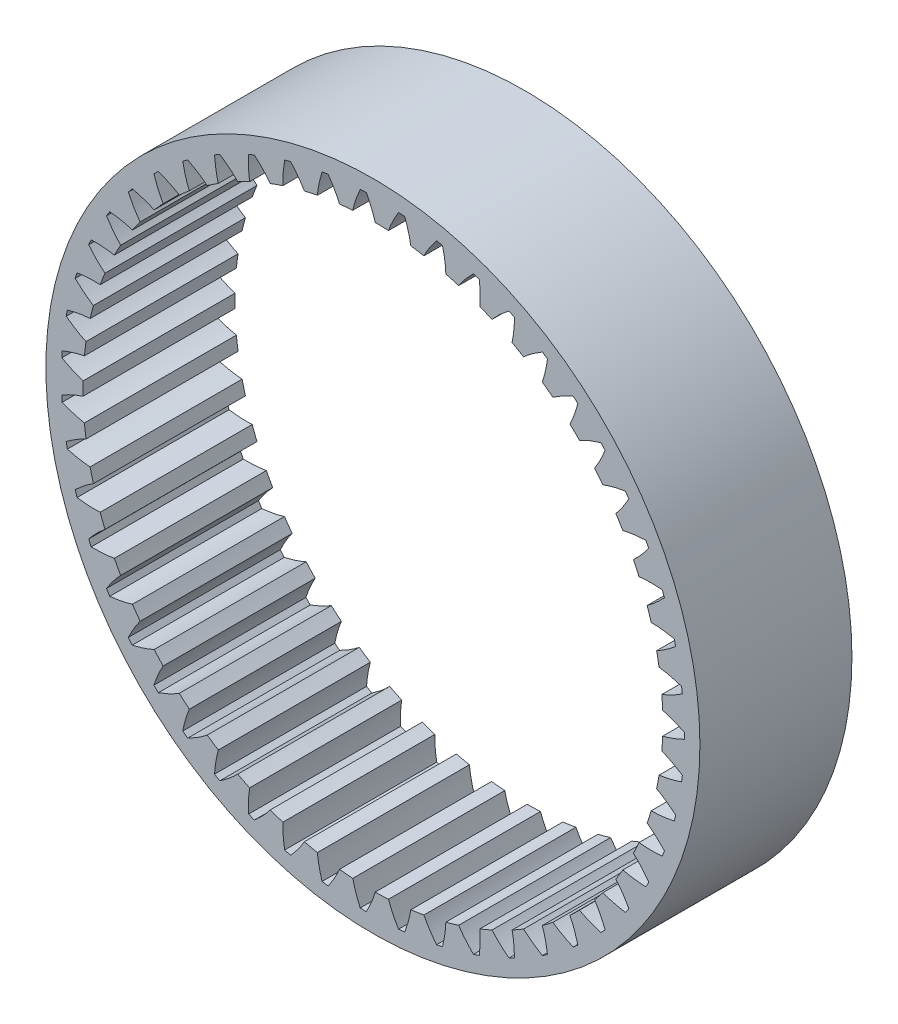
SolidWorks part; units mm, degrees
ref_plane "Front Plane" through (0, 0, 0) normal (0, 0, 1) x (1, 0, 0)
ref_plane "Top Plane" through (0, 0, 0) normal (0, 1, 0) x (1, 0, 0)
ref_plane "Right Plane" through (0, 0, 0) normal (1, 0, 0) x (0, 0, -1)
ref_axis "Axis1" through (0, 0, 6.9289) along (0, 0, -1)
sketch "Sketch3" plane through (0, 0, 0) normal (0, 0, 1) x (1, 0, 0)
  circle A0 centre (0, 0) radius 14.4132
  circle A1 centre (0, 0) radius 12.7793
  dimension "D1" = 28.8263
  dimension "D2" = 25.5585
extrude "Boss-Extrude2" add sketch "Sketch3" along normal blind 6.7
sketch "Sketch1" plane through (0, 0, 0) normal (0, 0, 1) x (1, 0, 0)
  line L8 (13.7262, 0.1357) -> (13.7262, -0.1357)
  line L10 (12.7697, 0.494) -> (12.7697, -0.494)
  circle A0 centre (0, 0) radius 12.7793 construction
  circle A1 centre (0, 0) radius 12.2733 construction
  circle A4 centre (0, 0) radius 13.7268 construction
  spline S0 degree 4 poles (12.6989, 0.5109) (12.704, 0.5097) (12.7137, 0.5075) (12.7273, 0.5044) (12.7616, 0.4961) (12.7786, 0.4918) (12.8216, 0.4809) (12.8476, 0.4738) (12.883, 0.464) (12.9127, 0.4555) (12.9457, 0.4458) (12.9766, 0.4364) (13.0087, 0.4264) (13.0399, 0.4163) (13.0716, 0.4059) (13.1027, 0.3954) (13.1342, 0.3846) (13.1723, 0.3711) (13.2188, 0.3542) (13.2716, 0.3344) (13.3337, 0.31) (13.3933, 0.286) (13.4571, 0.259) (13.5133, 0.2349) (13.5812, 0.2042) (13.629, 0.1825) (13.7046, 0.1463) (13.737, 0.1305) (13.7859, 0.1062) (13.8062, 0.0959) (13.8175, 0.0901) knots 0 0 0 0 0 0.01522 0.030441 0.060378 0.088008 0.115638 0.143268 0.170897 0.198527 0.226157 0.253787 0.281417 0.309046 0.336676 0.364306 0.391936 0.419565 0.472504 0.527763 0.583023 0.638282 0.693542 0.748801 0.804061 0.85932 0.91458 0.95729 1 1 1 1 1 construction
  spline S1 degree 4 poles (12.7697, 0.494) (12.7766, 0.4923) (12.79, 0.4889) (12.8216, 0.4809) (12.8476, 0.4738) (12.883, 0.464) (12.9127, 0.4555) (12.9457, 0.4458) (12.9766, 0.4364) (13.0087, 0.4264) (13.0399, 0.4163) (13.0716, 0.4059) (13.1027, 0.3954) (13.1342, 0.3846) (13.1723, 0.3711) (13.2188, 0.3542) (13.2716, 0.3344) (13.3337, 0.31) (13.3933, 0.286) (13.4571, 0.259) (13.5133, 0.2349) (13.5812, 0.2042) (13.629, 0.1825) (13.6891, 0.1537) (13.7135, 0.1419) (13.7262, 0.1357) knots 0.060378 0.060378 0.060378 0.060378 0.060378 0.088008 0.115638 0.143268 0.170897 0.198527 0.226157 0.253787 0.281417 0.309046 0.336676 0.364306 0.391936 0.419565 0.472504 0.527763 0.583023 0.638282 0.693542 0.748801 0.804061 0.85932 0.91458 0.91458 0.91458 0.91458 0.91458
  spline S2 degree 4 poles (12.6989, -0.5109) (12.704, -0.5097) (12.7137, -0.5075) (12.7273, -0.5044) (12.7616, -0.4961) (12.7786, -0.4918) (12.8216, -0.4809) (12.8476, -0.4738) (12.883, -0.464) (12.9127, -0.4555) (12.9457, -0.4458) (12.9766, -0.4364) (13.0087, -0.4264) (13.0399, -0.4163) (13.0716, -0.4059) (13.1027, -0.3954) (13.1342, -0.3846) (13.1723, -0.3711) (13.2188, -0.3542) (13.2716, -0.3344) (13.3337, -0.31) (13.3933, -0.286) (13.4571, -0.259) (13.5133, -0.2349) (13.5812, -0.2042) (13.629, -0.1825) (13.7046, -0.1463) (13.737, -0.1305) (13.7859, -0.1062) (13.8062, -0.0959) (13.8175, -0.0901) knots 0 0 0 0 0 0.01522 0.030441 0.060378 0.088008 0.115638 0.143268 0.170897 0.198527 0.226157 0.253787 0.281417 0.309046 0.336676 0.364306 0.391936 0.419565 0.472504 0.527763 0.583023 0.638282 0.693542 0.748801 0.804061 0.85932 0.91458 0.95729 1 1 1 1 1 construction
  spline S3 degree 4 poles (12.7697, -0.494) (12.7766, -0.4923) (12.79, -0.4889) (12.8216, -0.4809) (12.8476, -0.4738) (12.883, -0.464) (12.9127, -0.4555) (12.9457, -0.4458) (12.9766, -0.4364) (13.0087, -0.4264) (13.0399, -0.4163) (13.0716, -0.4059) (13.1027, -0.3954) (13.1342, -0.3846) (13.1723, -0.3711) (13.2188, -0.3542) (13.2716, -0.3344) (13.3337, -0.31) (13.3933, -0.286) (13.4571, -0.259) (13.5133, -0.2349) (13.5812, -0.2042) (13.629, -0.1825) (13.6891, -0.1537) (13.7135, -0.1419) (13.7262, -0.1357) knots 0.060378 0.060378 0.060378 0.060378 0.060378 0.088008 0.115638 0.143268 0.170897 0.198527 0.226157 0.253787 0.281417 0.309046 0.336676 0.364306 0.391936 0.419565 0.472504 0.527763 0.583023 0.638282 0.693542 0.748801 0.804061 0.85932 0.91458 0.91458 0.91458 0.91458 0.91458
  dimension "D1" = 25.5585
  dimension "D2" = 24.5466
  dimension "D3" = 27.4537
extrude "Cut-Extrude2" cut sketch "Sketch1" along normal through all
pattern_circular "CirPattern1" count 51 over 360 about axis through (0, 0, 6.9289) along (0, 0, -1) of "Cut-Extrude2"
sketch "Sketch4" plane through (0, 0, 0) normal (0, 0, 1) x (1, 0, 0)
  circle A0 centre (0, 0) radius 15
  circle A1 centre (0, 0) radius 14.4132
  dimension "D1" = 30
  dimension "D2" = 28.8263
extrude "width match" [suppressed] add sketch "Sketch4" along normal up to surface (6.7 mm away)
sketch "Sketch5" plane through (0, 0, 0) normal (0, 1, 0) x (1, 0, 0)
  line L0 (0, -6.9289) -> (0, 0.335) construction
  line L1 (10, -6.7) -> (15, -6.7)
  line L2 (10, -6.7) -> (10, -4.7)
  line L3 (10, -4.7) -> (15, -4.7)
  line L4 (15, -6.7) -> (15, -4.7)
  line L5 (15, 0) -> (16, 0)
  line L6 (15, 0) -> (15, -1)
  line L7 (15, -1) -> (16, -1)
  line L8 (16, 0) -> (16, -1)
  dimension "D1" = 15
  dimension "D2" = 1
  dimension "D3" = 1
  dimension "D4" = 15
  dimension "D5" = 6.7
  dimension "D6" = 4.7
  dimension "D7" = 5
revolve "Revolve1" [suppressed] add sketch "Sketch5" angle 360 about axis through (0, 0, 6.9289) along (0, 0, -1)
sketch "Sketch6" plane through (0, 0, 0) normal (0, 1, 0) x (1, 0, 0)
  line L0 (0, -6.9289) -> (0, 0.335) construction
  line L1 (14.75, -5.7) -> (15, -5.7)
  line L2 (14.75, -5.7) -> (14.75, -4.7)
  line L3 (14.75, -4.7) -> (15, -4.7)
  line L4 (15, -5.7) -> (15, -4.7)
  dimension "D1" = 4.7
  dimension "D2" = 1
  dimension "D3" = 0.25
  dimension "D4" = 15
revolve "Cut-Revolve1" [suppressed] cut sketch "Sketch6" angle 360 about axis through (0, 0, 6.9289) along (0, 0, -1)
sketch "Sketch7" [suppressed] plane through (0, 0, 6.7) normal (0, 0, 1) x (1, 0, 0)
  line L0 (0, 0) -> (12, 0) construction
  dimension "D1" = 12
sketch "Sketch8" [suppressed] plane through (0, 0, 6.7) normal (0, 0, 1) x (1, 0, 0)
  point P0 (12, 0)
hole_wizard "Tap Drill for M2x0.4 Tap1" [suppressed] positions "Sketch8" profile "Sketch9" hole size "M2x0.4" standard "ANSI Metric"
sketch "Sketch9" plane through (12, 0, 6.7) normal (1, 0, 0) x (0, -1, 0)
  line L0 (0, 0) -> (0, 6.7)
  line L1 (0, 6.7) -> (0.8, 6.7)
  line L2 (0.8, 6.7) -> (0.8, 0)
  line L5 (0.8, 0) -> (0, 0)
  line L11 (0, -6.35) -> (0, 107.95) construction
  dimension "Thru Hole Dia." = 1.6
  dimension "Thru Hole Depth" = 6.7
pattern_circular "CirPattern2" [suppressed] count 6 over 360 about axis through (0, 0, 6.9289) along (0, 0, -1)
equation "\"S1_Module\"= 0.5\t\t'tooth per mm"
equation "\"R1_NumTeeth\"= 52"
equation "\"R2_teeth\"= 51"
equation "\"P1_teeth\"= 10"
equation "\"S1_PressureAngle\"= 20'deg. leave unitless"
equation "\"sun_teeth\"= \"R1_NumTeeth\" - 2 * \"P1_teeth\""
equation "\"S2_Module\"= 0.5121951219512195\t\t\t'stage two gear modules CAN be different from stage 1; this makes things a lot more complicated though so try and avoid it if you can"
equation "\"S2_PressureAngle\"= \"S1_PressureAngle\"'stage two pressure angle can be different, but for simplicity keep it the same"
equation "\"S1_carrier_radius\"= \"P1_teeth\" * \"S1_Module\" / 2  + \"sun_teeth\" * \"S1_Module\" / 2"
equation "\"P2_teeth\" = 10"
equation "\"Ring_profile_shift\" = 0.05"
equation "\"Planet_profile_shift\" = -0.05"
equation "\"Planet_broachcutter_offset\" = -0.0"
equation "\"Ring_broachcutter_offset\" = 0.0"
equation "\"Nteeth_bcg\"= \"R2_teeth\""
equation "\"module\"= \"S2_Module\""
equation "\"x_shift\"= \"Ring_profile_shift\""
equation "\"r_p_bcg\"= \"module\" * \"Nteeth_bcg\" / 2"
equation "\"head\"= - 0.4 'Default. A clearance parameter applied to the addendum in internal gears. Removes material for clearance"
equation "\"r_a_bcg\"= \"r_p_bcg\" - \"module\" * ( 1 - \"x_shift\" + \"head\" )"
equation "\"r_f_bcg\"= \"r_p_bcg\" + \"module\" * ( 1.25 + \"x_shift\" )"
equation "\"Nteeth\"= \"R2_teeth\""
equation "\"pressure_angle\"= \"S1_PressureAngle\" * pi / 180"
equation "\"r_p\"= \"module\" * \"Nteeth\" / 2'pitch circle radius"
equation "\"r_b\"= \"r_p\" * cos ( \"pressure_angle\" )'base circle radius"
equation "\"r_f\"= \"r_p\" + \"module\" * ( 1.25 + \"x_shift\" )"
equation "\"r_a\"= \"r_p\" - \"module\" * ( 1 - \"x_shift\" + \"head\" ) 'addendum"
equation "\"ttoaddendum\"= sqr ( ( \"r_a\" / \"r_b\" ) * ( \"r_a\" / \"r_b\" ) - 1 )"
equation "\"tmax\"= sqr ( ( \"r_f\" / \"r_b\" ) * ( \"r_f\" / \"r_b\" ) - 1 )"
equation "\"toothoffset\"= pi / \"Nteeth\"'Kludge. If odd number of teeth, remove the *0. If even, add a *0. Its to clock the midplane to the void between teeth for alignment in planetary stacks"
equation "\"t_p\"= sqr ( ( \"r_p\" / \"r_b\" ) ^ 2 - 1 )'t at pitch circle"
equation "\"x_p\"= \"r_b\" * ( cos ( \"t_p\" ) + \"t_p\" * sin ( \"t_p\" ) )"
equation "\"y_p\"= \"r_b\" * ( sin ( \"t_p\" ) - \"t_p\" * cos ( \"t_p\" ) )"
equation "\"theta_p\"= atn ( \"y_p\" / \"x_p\" )"
equation "\"des_ang\"= ( pi / 2 - 2 * \"x_shift\" * tan ( \"pressure_angle\" ) ) / \"Nteeth\""
equation "\"delta\"= \"des_ang\" - \"theta_p\""
equation "\"delta2\"= \"delta\" + 2 * pi * ( \"Nteeth\" - 1 ) / \"Nteeth\""
equation "\"height\"=6.7"
equation "\"involute_offset\"= - \"r_a\" + \"r_a_bcg\" + \"Ring_broachcutter_offset\" 'Hit CTL+q after changing this or it wont update properly"
equation "\"D1@Sketch1\"=\"r_a\"*2"
equation "\"D2@Sketch1\"=\"r_b\"*2"
equation "\"D1@Sketch3\"=\"r_f_bcg\"*2.1"
equation "\"D2@Sketch3\"=(\"r_a\"+\"involute_offset\")*2"
equation "\"D3@Sketch1\"=\"r_f\"*2"
equation "\"D1@CirPattern1\"=\"Nteeth_bcg\""
equation "\"D1@Boss-Extrude2\"=\"height\""
equation "\"D2@Sketch4\"=\"r_f_bcg\"*2.1"
